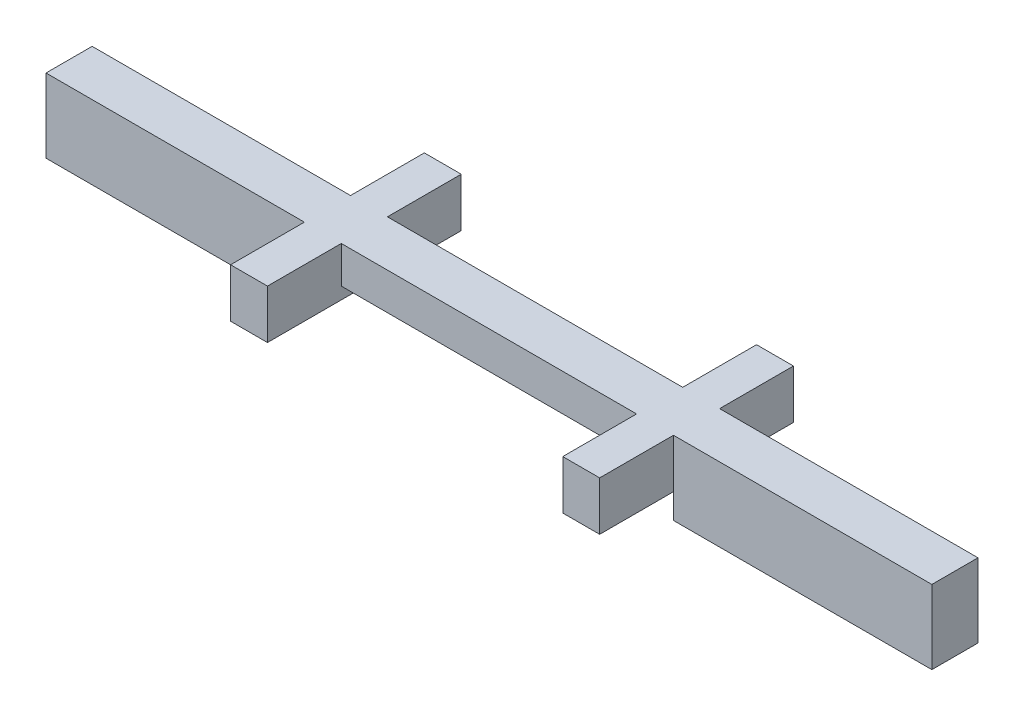
SolidWorks part; units mm, degrees
ref_plane "Front Plane" through (0, 0, 0) normal (0, 0, 1) x (1, 0, 0)
ref_plane "Top Plane" through (0, 0, 0) normal (0, 1, 0) x (1, 0, 0)
ref_plane "Right Plane" through (0, 0, 0) normal (1, 0, 0) x (0, 0, -1)
sketch "Sketch1" plane through (0, 0, 0) normal (0, 0, 1) x (1, 0, 0)
  line L10 (1, 0) -> (9, 0)
  line L12 (0, 1) -> (10, 1)
  line L14 (0, 1) -> (-7, 1)
  line L15 (0, -0.325) -> (0, -1)
  line L16 (0, -1) -> (-7, -1)
  line L17 (-7, 1) -> (-7, -1)
  line L18 (10, 1) -> (17, 1)
  line L19 (10, -0.325) -> (10, -1)
  line L20 (10, -1) -> (17, -1)
  line L21 (17, 1) -> (17, -1)
  line L24 (0, -0.325) -> (1, -0.325)
  line L25 (1, 0) -> (1, -0.325)
  line L28 (10, -0.325) -> (9, -0.325)
  line L29 (9, 0) -> (9, -0.325)
extrude "Boss-Extrude1" add sketch "Sketch1" along normal blind 1.25
sketch "Sketch4" plane through (0, 0, 0) normal (0, 0, -1) x (-1, 0, 0)
  line L0 (-17, 1) -> (7, 1) construction
  line L1 (-9, -0.325) -> (-10, -0.325)
  line L2 (-9, -0.325) -> (-9, 1)
  line L3 (-9, 1) -> (-10, 1)
  line L4 (-10, -0.325) -> (-10, 1)
  line L6 (-1, -0.325) -> (0, -0.325)
  line L7 (-1, -0.325) -> (-1, 1)
  line L8 (-1, 1) -> (0, 1)
  line L9 (0, -0.325) -> (0, 1)
  dimension "D1" = 1
  dimension "D2" = 1
extrude "Boss-Extrude4" add sketch "Sketch4" along normal blind 2
sketch "Sketch5" plane through (0, 0, 1.25) normal (0, 0, 1) x (1, 0, 0)
  line L0 (17, 1) -> (-7, 1) construction
  line L1 (1, -0.325) -> (0, -0.325)
  line L2 (1, -0.325) -> (1, 1)
  line L3 (1, 1) -> (0, 1)
  line L4 (0, -0.325) -> (0, 1)
  line L6 (9, -0.325) -> (10, -0.325)
  line L7 (9, -0.325) -> (9, 1)
  line L8 (9, 1) -> (10, 1)
  line L9 (10, -0.325) -> (10, 1)
  dimension "D1" = 1
  dimension "D2" = 1
extrude "Boss-Extrude5" add sketch "Sketch5" along normal blind 2
